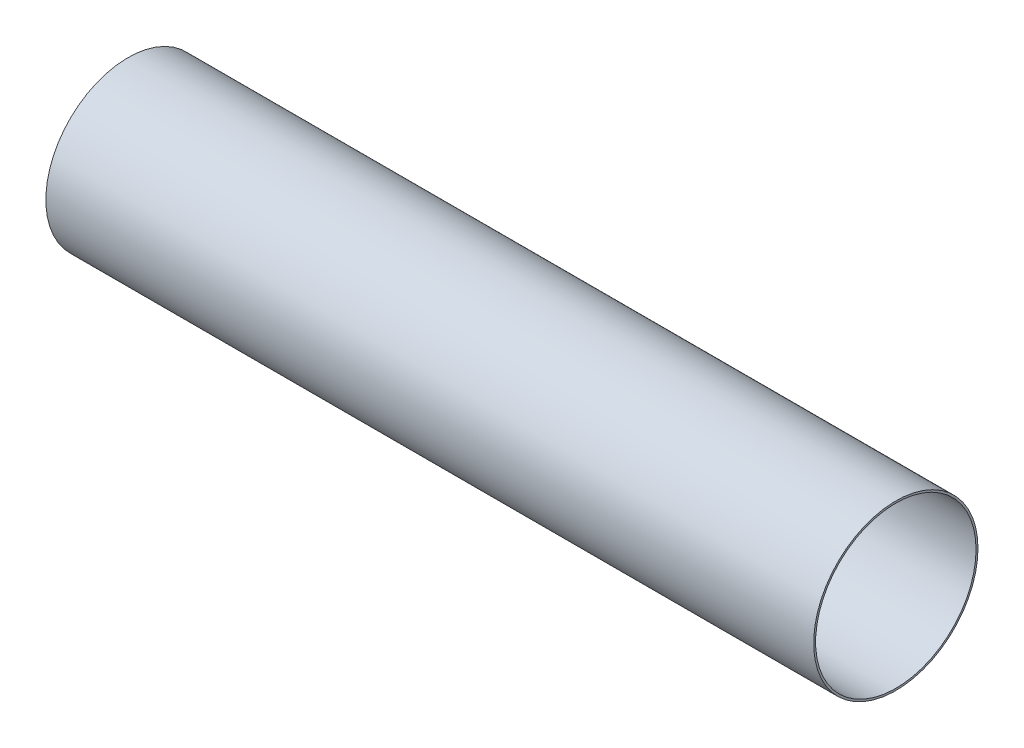
SolidWorks part; units mm, degrees
material "Thornel Mat VMA"
ref_plane "Front Plane" through (0, 0, 0) normal (0, 0, 1) x (1, 0, 0)
ref_plane "Top Plane" through (0, 0, 0) normal (0, 1, 0) x (1, 0, 0)
ref_plane "Right Plane" through (0, 0, 0) normal (1, 0, 0) x (0, 0, -1)
sketch "Sketch1" plane through (0, 0, 0) normal (1, 0, 0) x (0, 0, -1)
  circle A0 centre (0, 0) radius 84.55
  dimension "D1" = 169.1
extrude "Boss-Extrude2" add sketch "Sketch1" along normal blind 790 contours A0
sketch "Sketch3" plane through (790, 0, 0) normal (1, 0, 0) x (0, 0, -1)
  circle A0 centre (0, 0) radius 82.55
  dimension "D1" = 165.1
extrude "Cut-Extrude1" cut sketch "Sketch3" against normal blind 940
